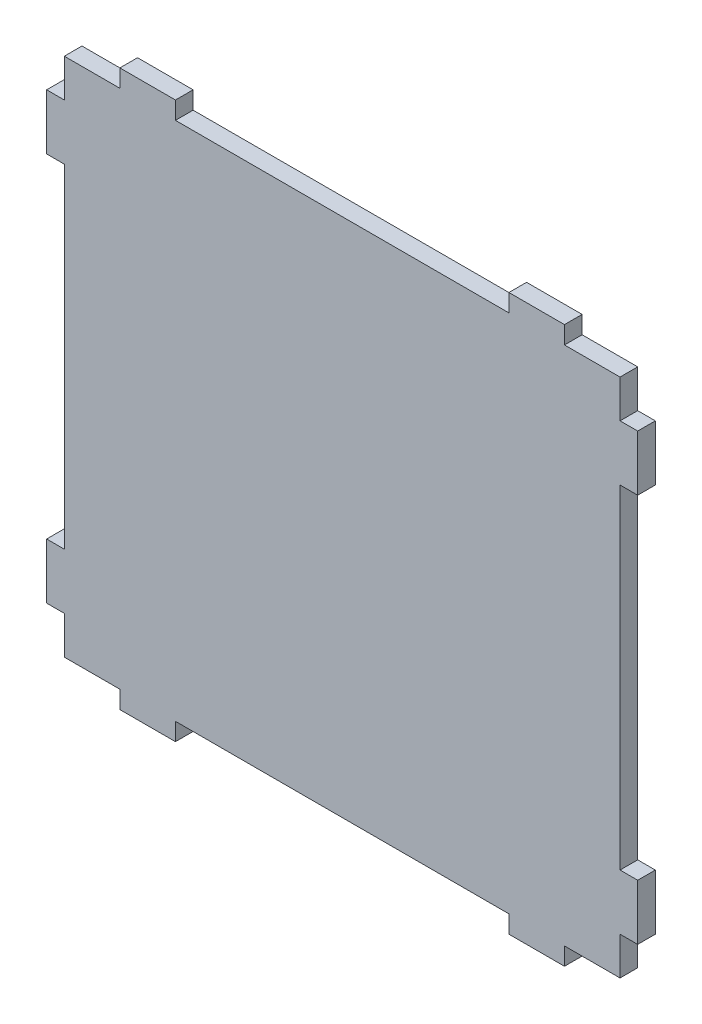
SolidWorks part; units mm, degrees
ref_plane "Front Plane" through (0, 0, 0) normal (0, 0, 1) x (1, 0, 0)
ref_plane "Top Plane" through (0, 0, 0) normal (0, 1, 0) x (1, 0, 0)
ref_plane "Right Plane" through (0, 0, 0) normal (1, 0, 0) x (0, 0, -1)
sketch "Sketch1" plane through (0, 0, 0) normal (0, 0, 1) x (1, 0, 0)
  line L0 (10, 3.175) -> (0, 3.175)
  line L1 (0, 0) -> (100, 0) construction
  line L2 (0, 0) -> (0, 100) construction
  line L3 (0, 100) -> (100, 100) construction
  line L4 (100, 0) -> (100, 100) construction
  line L5 (90, 96.825) -> (100, 96.825)
  line L6 (3.175, 96.825) -> (96.825, 96.825) construction
  line L7 (3.175, 3.175) -> (3.175, 96.825) construction
  line L8 (50, 96.825) -> (50, 60.4614) construction
  line L9 (10, 96.825) -> (0, 96.825)
  line L10 (10, 96.825) -> (10, 100)
  line L11 (10, 100) -> (20, 100)
  line L12 (20, 96.825) -> (20, 100)
  line L13 (3.175, 50) -> (74.6982, 50) construction
  line L14 (20, 96.825) -> (80, 96.825)
  line L15 (90, 3.175) -> (100, 3.175)
  line L16 (80, 96.825) -> (80, 100)
  line L17 (90, 100) -> (80, 100)
  line L18 (90, 96.825) -> (90, 100)
  line L19 (3.175, 3.175) -> (96.825, 3.175) construction
  line L20 (0, 90) -> (0, 96.825)
  line L21 (90, 3.175) -> (90, 0)
  line L22 (90, 0) -> (80, 0)
  line L23 (80, 3.175) -> (80, 0)
  line L24 (20, 3.175) -> (80, 3.175)
  line L25 (20, 3.175) -> (20, 0)
  line L26 (10, 0) -> (20, 0)
  line L27 (10, 3.175) -> (10, 0)
  line L28 (0, 90) -> (-3.175, 90)
  line L29 (0, 80) -> (0, 20)
  line L30 (0, 80) -> (-3.175, 80)
  line L31 (-3.175, 90) -> (-3.175, 80)
  line L32 (-3.175, 10) -> (-3.175, 20)
  line L33 (96.825, 3.175) -> (96.825, 96.825) construction
  line L34 (0, 20) -> (-3.175, 20)
  line L35 (0, 10) -> (-3.175, 10)
  line L36 (0, 10) -> (0, 3.175)
  line L37 (100, 90) -> (100, 96.825)
  line L38 (100, 10) -> (100, 3.175)
  line L39 (100, 10) -> (103.175, 10)
  line L40 (100, 20) -> (103.175, 20)
  line L41 (103.175, 10) -> (103.175, 20)
  line L42 (103.175, 90) -> (103.175, 80)
  line L43 (100, 80) -> (103.175, 80)
  line L44 (100, 80) -> (100, 20)
  line L45 (100, 90) -> (103.175, 90)
  point P20 (50, 96.825)
  point P24 (93.4125, 3.175)
  point P32 (50, 3.175)
  point P44 (0, 50)
  point P53 (100, 50)
  dimension "D1" = 100
  dimension "D2" = 100
  dimension "D4" = 10
  dimension "D5" = 3.175
  dimension "D6" = 10
  dimension "D7" = 10
  dimension "D8" = 3.175
  dimension "D9" = 10
  dimension "D3" = 3.175
extrude "Boss-Extrude1" add sketch "Sketch1" along normal blind 3.175
